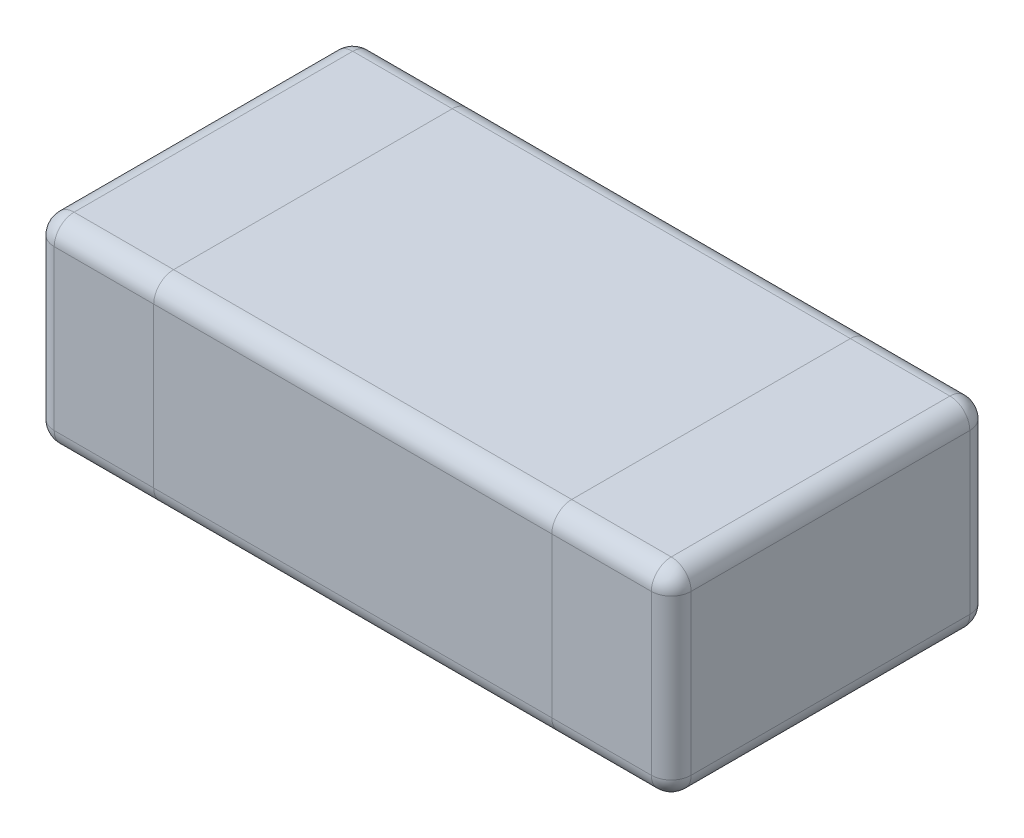
SolidWorks part; units mm, degrees
ref_plane "Front Plane" through (0, 0, 0) normal (0, 0, 1) x (1, 0, 0)
ref_plane "Top Plane" through (0, 0, 0) normal (0, 1, 0) x (1, 0, 0)
ref_plane "Right Plane" through (0, 0, 0) normal (1, 0, 0) x (0, 0, -1)
sketch "Sketch1" plane through (0, 0, 0) normal (0, 1, 0) x (1, 0, 0)
  line L1 (0, 0) -> (0.3, 0)
  line L2 (0, 0) -> (0, 0.8)
  line L3 (0, 0.8) -> (0.3, 0.8)
  line L4 (0.3, 0) -> (0.3, 0.8)
  line L5 (0.15, 0.8) -> (0.15, 0) construction
  line L6 (0, 0.4) -> (0.3, 0.4) construction
  line L7 (1.3, 0.8) -> (1.6, 0.8)
  line L8 (1.3, 0.8) -> (1.3, 0)
  line L9 (1.3, 0) -> (1.6, 0)
  line L10 (1.6, 0.8) -> (1.6, 0)
  line L11 (1.45, 0) -> (1.45, 0.8) construction
  line L12 (1.3, 0.4) -> (1.6, 0.4) construction
  point P112 (0.15, 0.4)
  point P158 (1.45, 0.4)
  dimension "D1" = 0.8
  dimension "D2" = 0.8
  dimension "D3" = 1.6
  dimension "D4" = 0.3
  dimension "D5" = 0.3
extrude "Boss-Extrude1" add sketch "Sketch1" along normal blind 0.5
sketch "Sketch2" plane through (0, 0, 0) normal (0, 1, 0) x (1, 0, 0)
  line L1 (0.3, 0.8) -> (1.3, 0.8)
  line L2 (0.3, 0.8) -> (0.3, 0)
  line L3 (0.3, 0) -> (1.3, 0)
  line L4 (1.3, 0.8) -> (1.3, 0)
  line L5 (0.8, 0) -> (0.8, 0.8) construction
  line L6 (0.3, 0.4) -> (1.3, 0.4) construction
  point P132 (0.8, 0.4)
extrude "Boss-Extrude2" add sketch "Sketch2" along normal blind 0.5 separate body
sketch "Sketch3" [suppressed] plane through (0, 0.5, 0) normal (0, 1, 0) x (1, 0, 0)
  line L0 (0.3, 0) -> (1.3, 0) construction
  line L1 (0, 0.8) -> (0, 0) construction
  point P0 (0.8, 0.4)
  dimension "D1" = 0.4
  dimension "D2" = 0.8
fillet "Fillet1" radius 0.05 8 edges at (0, 0.25, -0.8) (0, 0.5, -0.4) (0, 0.25, 0) (0, 0, -0.4) (0.15, 0, -0.8) (0.15, 0, 0) (0.15, 0.5, -0.8) (0.15, 0.5, 0)
fillet "Fillet2" radius 0.05 8 edges at (1.6, 0.25, 0) (1.6, 0.5, -0.4) (1.6, 0.25, -0.8) (1.6, 0, -0.4) (1.45, 0, 0) (1.45, 0.5, 0) (1.45, 0, -0.8) (1.45, 0.5, -0.8)
fillet "Fillet3" radius 0.05 4 edges at (0.8, 0, 0) (0.8, 0, -0.8) (0.8, 0.5, -0.8) (0.8, 0.5, 0)
